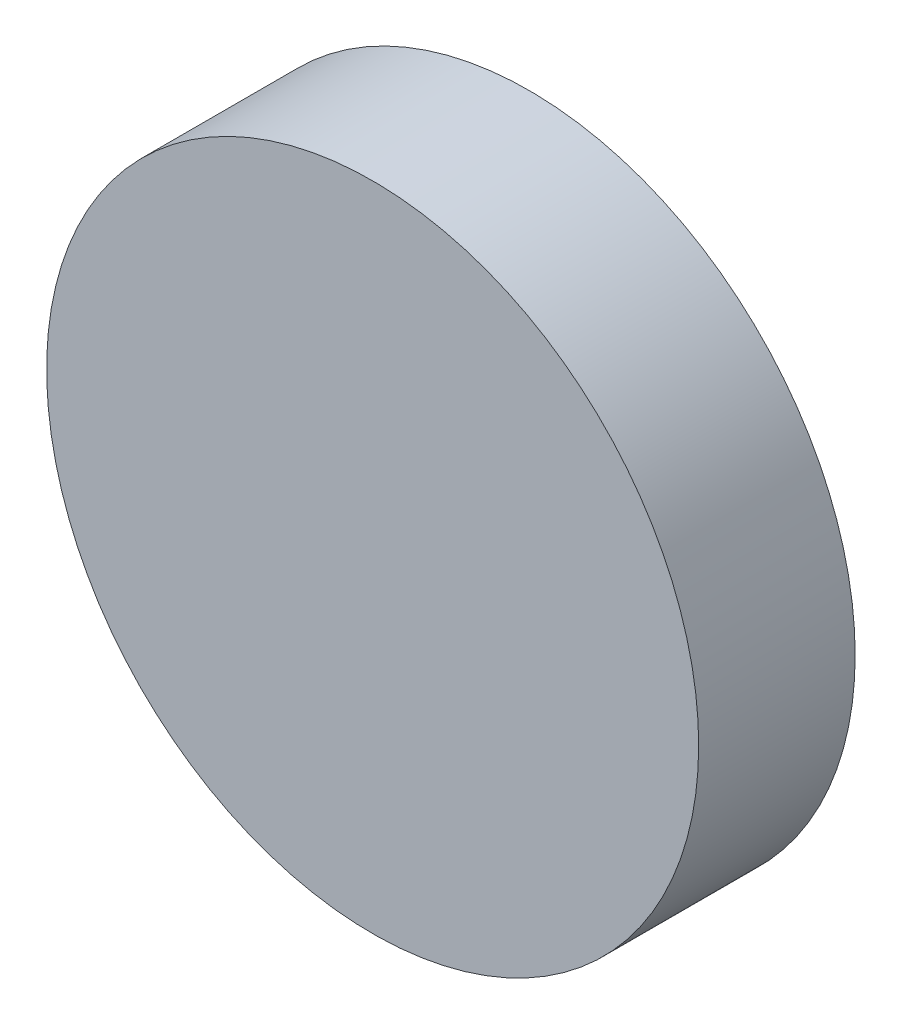
SolidWorks part; units mm, degrees
ref_plane "前视基准面" through (0, 0, 0) normal (0, 0, 1) x (1, 0, 0)
ref_plane "上视基准面" through (0, 0, 0) normal (0, 1, 0) x (1, 0, 0)
ref_plane "右视基准面" through (0, 0, 0) normal (1, 0, 0) x (0, 0, -1)
sketch "草图1" plane through (0, 0, 0) normal (0, 0, 1) x (1, 0, 0)
  circle A0 centre (0, 0) radius 6.25
extrude "凸台-拉伸1" add sketch "草图1" along normal blind 3
